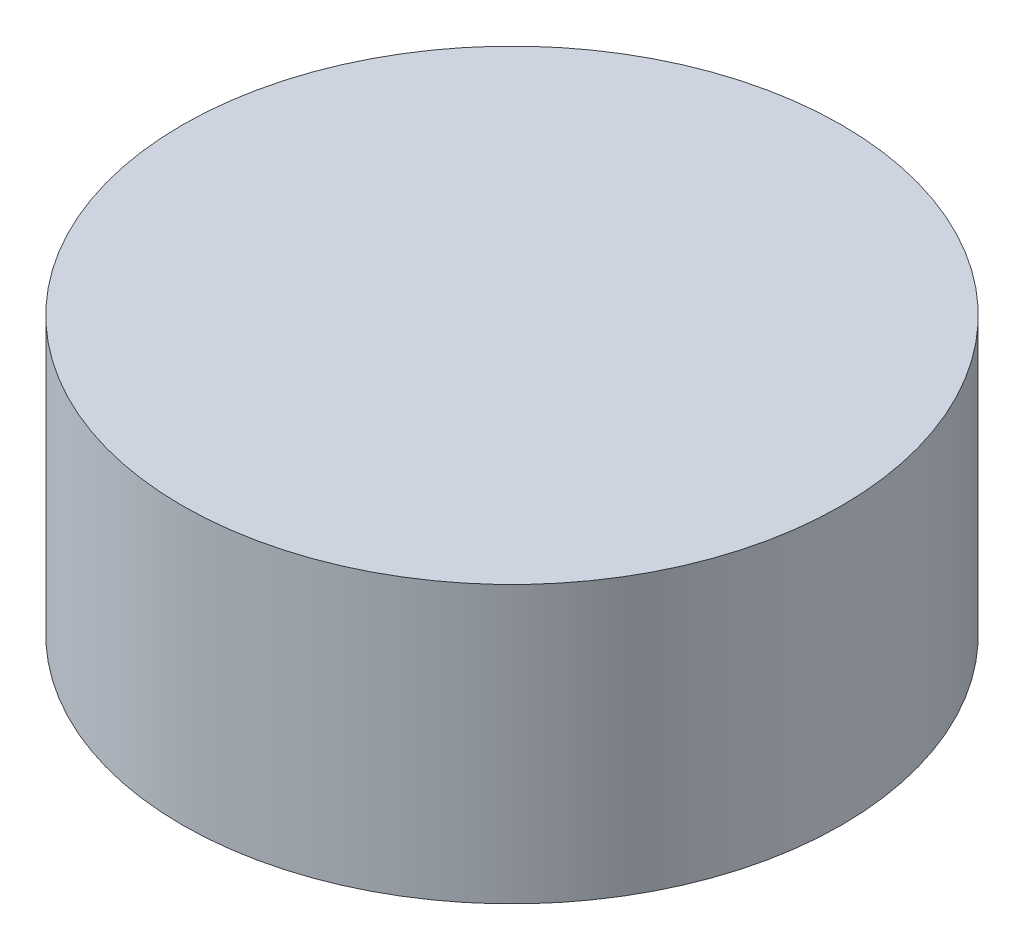
SolidWorks part; units mm, degrees
ref_plane "Front Plane" through (0, 0, 0) normal (0, 0, 1) x (1, 0, 0)
ref_plane "Top Plane" through (0, 0, 0) normal (0, 1, 0) x (1, 0, 0)
ref_plane "Right Plane" through (0, 0, 0) normal (1, 0, 0) x (0, 0, -1)
sketch "Sketch2" plane through (0, 0, 0) normal (0, 0, 1) x (1, 0, 0)
  line L0 (-2765, 500) -> (-7000, 500)
  line L2 (-2765, 500) -> (-2765, 2735.8742)
  line L3 (-2765, 2735.8742) -> (-2133.6, 3342)
  line L4 (-2133.6, 3342) -> (0, 3342)
  line L5 (0, 3342) -> (0, 3372)
  line L6 (0, 3372) -> (-7000, 3372)
  line L7 (-7000, 3372) -> (-7000, 500)
  dimension "D1" = 3342
  dimension "D2" = 7000
  dimension "D3" = 30
  dimension "D4" = 500
  dimension "D5" = 2133.6
  dimension "D6" = 136.17
  dimension "D8" = 2765
ref_axis "Axis1" through (0, 3520.44, 0) along (0, -1, 0)
revolve "Revolve2" add sketch "Sketch2" angle 360 about axis through (0, 3520.44, 0) along (0, -1, 0)
sketch "Sketch3" plane through (0, 0, 0) normal (1, 0, 0) x (0, 0, -1)
  line L1 (-7000, 500) -> (-3750, 500)
  line L2 (-7000, 500) -> (-7000, -2500)
  line L3 (-7000, -2500) -> (-3750, -2500)
  line L4 (-3750, 500) -> (-3750, -2500)
  dimension "D1" = 3750
  dimension "D2" = 3000
revolve "Revolve3" add sketch "Sketch3" angle 360 about axis through (0, 3520.44, 0) along (0, -1, 0)
